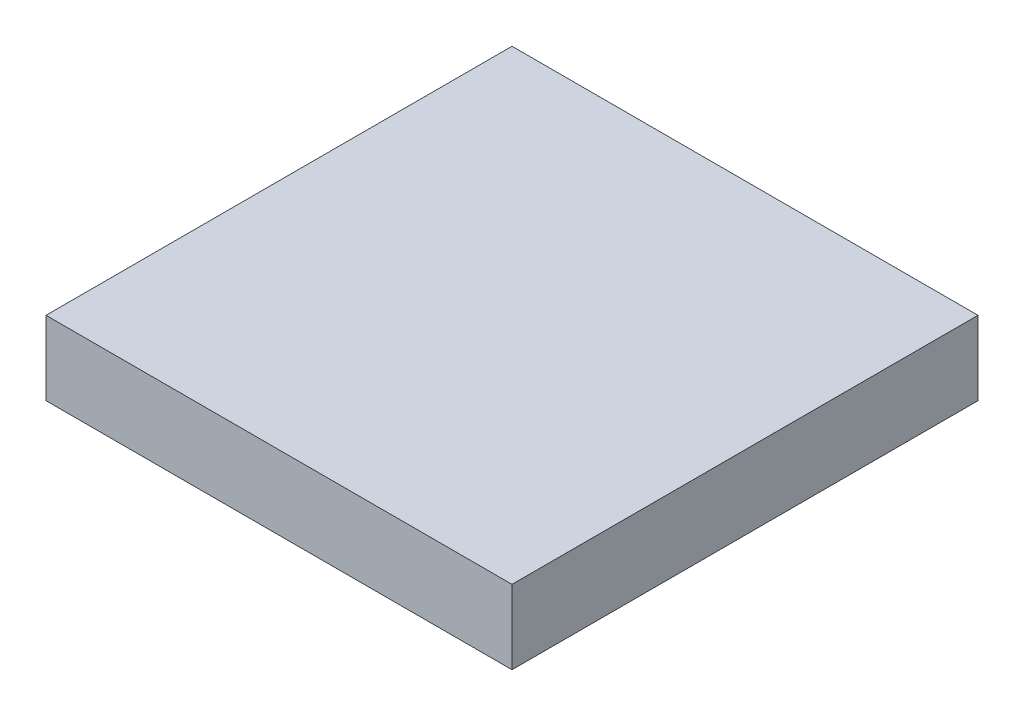
SolidWorks part; units mm, degrees
ref_plane "Front Plane" through (0, 0, 0) normal (0, 0, 1) x (1, 0, 0)
ref_plane "Top Plane" through (0, 0, 0) normal (0, 1, 0) x (1, 0, 0)
ref_plane "Right Plane" through (0, 0, 0) normal (1, 0, 0) x (0, 0, -1)
sketch "Sketch1" plane through (0, 0, 0) normal (0, 1, 0) x (1, 0, 0)
  line L1 (0, 0) -> (80.01, 0)
  line L2 (0, 0) -> (0, -80.01)
  line L3 (0, -80.01) -> (80.01, -80.01)
  line L4 (80.01, 0) -> (80.01, -80.01)
  dimension "D1" = 80.01
  dimension "D2" = 80.01
extrude "Boss-Extrude1" add sketch "Sketch1" along normal blind 12.7
